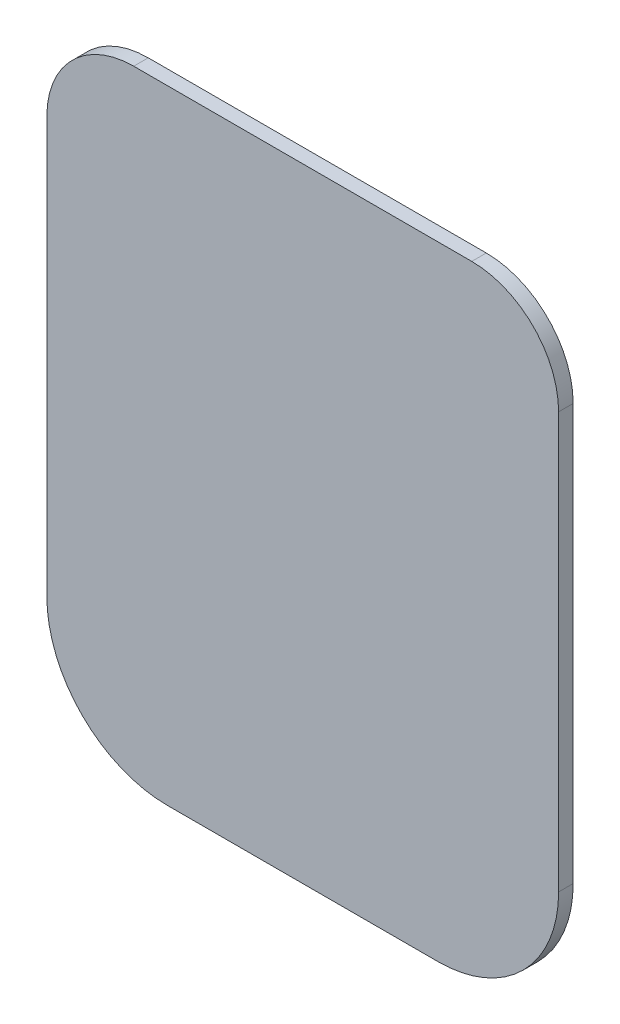
SolidWorks part; units mm, degrees
ref_plane "Front Plane" through (0, 0, 0) normal (0, 0, 1) x (1, 0, 0)
ref_plane "Top Plane" through (0, 0, 0) normal (0, 1, 0) x (1, 0, 0)
ref_plane "Right Plane" through (0, 0, 0) normal (1, 0, 0) x (0, 0, -1)
sketch "Sketch1" plane through (0, 0, 0) normal (0, 0, 1) x (1, 0, 0)
  line L0 (0, 96.5) -> (0, -96.5) construction
  line L1 (-80, 96.5) -> (80, 96.5) construction
  line L2 (-80, 96.5) -> (-80, -96.5) construction
  line L3 (-80, -96.5) -> (80, -96.5) construction
  line L4 (80, 96.5) -> (80, -96.5) construction
  line L5 (-50, 96.5) -> (50, 96.5) construction
  line L6 (-40, -96.5) -> (40, -96.5) construction
  line L7 (-80, 66.5) -> (80, 66.5) construction
  line L8 (-80, 66.5) -> (-80, -56.5) construction
  line L9 (-80, -56.5) -> (80, -56.5) construction
  line L10 (80, 66.5) -> (80, -56.5) construction
  line L11 (-0.5, -96.5) -> (0.5, -96.5) construction
  line L12 (-40, -96.5) -> (-0.5, -96.5) construction
  line L13 (0.5, -96.5) -> (40, -96.5) construction
  line L14 (0.5, -92.2) -> (40, -92.2)
  line L15 (75.7, 66.5) -> (75.7, -56.5)
  line L16 (-50, 92.2) -> (50, 92.2)
  line L17 (-75.7, 66.5) -> (-75.7, -56.5)
  line L18 (-40, -92.2) -> (-0.5, -92.2)
  line L19 (-0.5, -92.2) -> (0.5, -92.2)
  arc A0 (-80, 66.5) -> (-50, 96.5) centre (-50, 66.5) cw construction
  arc A1 (50, 96.5) -> (80, 66.5) centre (50, 66.5) cw construction
  arc A2 (-80, -56.5) -> (-40, -96.5) centre (-40, -56.5) ccw construction
  arc A3 (40, -96.5) -> (80, -56.5) centre (40, -56.5) ccw construction
  arc A4 (40, -92.2) -> (75.7, -56.5) centre (40, -56.5) ccw
  arc A5 (50, 92.2) -> (75.7, 66.5) centre (50, 66.5) cw
  arc A6 (-75.7, 66.5) -> (-50, 92.2) centre (-50, 66.5) cw
  arc A7 (-75.7, -56.5) -> (-40, -92.2) centre (-40, -56.5) ccw
  point P6 (0, 0)
  point P10 (0, 96.5)
  point P19 (0, -96.5)
  point P23 (0, -96.5)
  dimension "D3" = 40
  dimension "D4" = 30
  dimension "D1" = 193
  dimension "D2" = 160
  dimension "D5" = 1
  dimension "D6" = 4.3
extrude "Boss-Extrude1" add sketch "Sketch1" along normal blind 4.3
sketch "Sketch2" plane through (0, 0, 4.3) normal (0, 0, 1) x (1, 0, 0)
  line L0 (-40, -92.2) -> (40, -92.2) construction
  line L1 (-39.555, 35.11) -> (39.555, 35.11)
  line L2 (-39.555, 35.11) -> (-39.555, -54.89)
  line L3 (-39.555, -54.89) -> (39.555, -54.89)
  line L4 (39.555, 35.11) -> (39.555, -54.89)
  line L6 (-30, -54.89) -> (30, -54.89)
  line L7 (-30, -54.89) -> (-30, -59.19)
  line L8 (-30, -59.19) -> (30, -59.19)
  line L9 (30, -54.89) -> (30, -59.19)
  line L10 (-30, -59.19) -> (-25.7, -59.19)
  line L11 (-30, -59.19) -> (-30, -92.2)
  line L12 (-30, -92.2) -> (-25.7, -92.2)
  line L13 (-25.7, -59.19) -> (-25.7, -92.2)
  line L14 (30, -59.19) -> (25.7, -59.19)
  line L15 (30, -59.19) -> (30, -92.2)
  line L16 (30, -92.2) -> (25.7, -92.2)
  line L17 (25.7, -59.19) -> (25.7, -92.2)
  point P4 (0, -54.89)
  point P18 (0, -59.19)
  line M5 (-40, -92.2) -> (40, -92.2)
  dimension "D1" = 90
  dimension "D2" = 79.11
  dimension "D3" = 37.31
  dimension "D4" = 4.3
  dimension "D5" = 4.3
  dimension "D6" = 60
  dimension "D7" = 4.3
extrude "Cut-Extrude1" [suppressed] cut sketch "Sketch2" against normal blind 10 contours L4 L1 L2 L3 | L9 L3 L7 L8 | L13 L8 L11 M5 | L8 L17 L15 M5
